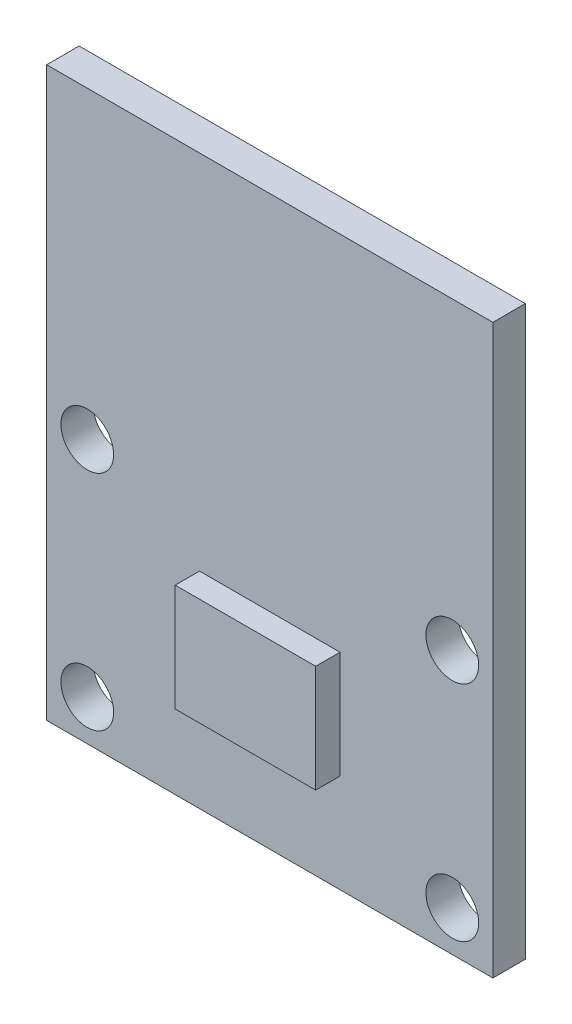
SolidWorks part; units mm, degrees
ref_plane "Front Plane" through (0, 0, 0) normal (0, 0, 1) x (1, 0, 0)
ref_plane "Top Plane" through (0, 0, 0) normal (0, 1, 0) x (1, 0, 0)
ref_plane "Right Plane" through (0, 0, 0) normal (1, 0, 0) x (0, 0, -1)
sketch "Sketch1" plane through (0, 0, 0) normal (0, 0, 1) x (1, 0, 0)
  line L1 (-11, 14) -> (11, 14)
  line L2 (-11, 14) -> (-11, -14)
  line L3 (-11, -14) -> (11, -14)
  line L4 (11, 14) -> (11, -14)
  line L5 (-11, 14) -> (11, -14) construction
  line L6 (-11, -14) -> (11, 14) construction
  circle A0 centre (-9, -12) radius 1.3
  circle A1 centre (9, -12) radius 1.3
  circle A2 centre (-9, -1) radius 1.3
  circle A3 centre (9, -1) radius 1.3
  point P0 (0, 0)
  dimension "D3" = 2.6
  dimension "D4" = 2.6
  dimension "D5" = 9
  dimension "D6" = 9
  dimension "D7" = 11
  dimension "D8" = 11
  dimension "D9" = 2.6
  dimension "D10" = 2.6
  dimension "D11" = 0
  dimension "D12" = 0
  dimension "D13" = 0
  dimension "D14" = 2
  dimension "D1" = 22
  dimension "D2" = 28
extrude "Boss-Extrude1" add sketch "Sketch1" along normal blind 1.6
sketch "Sketch2" plane through (0, 0, 1.6) normal (0, 0, 1) x (1, 0, 0)
  line L0 (-9, -1) -> (9, -12) construction
  line L1 (9, -1) -> (-9, -12) construction
  line L3 (-3.4634, -3.8552) -> (3.4634, -3.8552)
  line L4 (-3.4634, -3.8552) -> (-3.4634, -9.1448)
  line L5 (-3.4634, -9.1448) -> (3.4634, -9.1448)
  line L6 (3.4634, -3.8552) -> (3.4634, -9.1448)
  line L7 (-3.4634, -3.8552) -> (3.4634, -9.1448) construction
  line L8 (-3.4634, -9.1448) -> (3.4634, -3.8552) construction
  point P8 (0, -6.5)
  point P9 (0, -6.5)
extrude "Boss-Extrude2" add sketch "Sketch2" along normal blind 1.2
ref_point "Point1"
